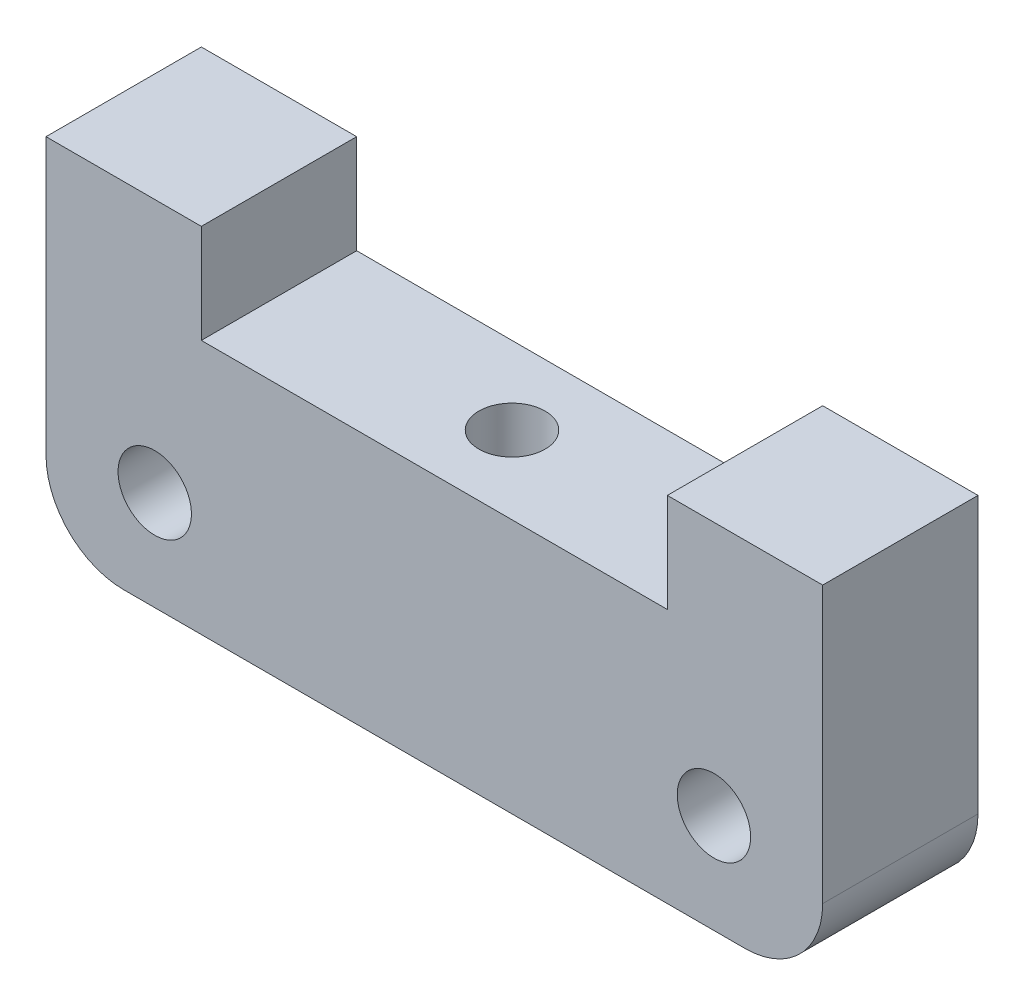
SolidWorks part; units mm, degrees
ref_plane "Front Plane" through (0, 0, 0) normal (0, 0, 1) x (1, 0, 0)
ref_plane "Top Plane" through (0, 0, 0) normal (0, 1, 0) x (1, 0, 0)
ref_plane "Right Plane" through (0, 0, 0) normal (1, 0, 0) x (0, 0, -1)
sketch "Sketch1" plane through (0, 0, 0) normal (0, 0, 1) x (1, 0, 0)
  line L0 (0, 0) -> (15.875, 0)
  line L1 (15.875, 0) -> (15.875, 14.4526)
  line L2 (15.875, 14.4526) -> (9.525, 14.4526)
  line L3 (9.525, 14.4526) -> (9.525, 10.414)
  line L4 (9.525, 10.414) -> (0, 10.414)
  line L5 (0, 10.414) -> (0, 0) construction
  line L6 (0, 10.414) -> (0, 0)
  circle A0 centre (11.43, 4.064) radius 1.5
  dimension "D1" = 3
  dimension "D2" = 4.064
  dimension "D3" = 19.05
  dimension "D4" = 6.35
  dimension "D5" = 22.86
  dimension "D6" = 4.0386
  dimension "D7" = 6.35
extrude "Boss-Extrude1" add sketch "Sketch1" along normal blind 6.35
mirror "Mirror1" about plane through (0, 10.414, 6.35) normal (1, 0, 0) of "Boss-Extrude1"
sketch "Sketch2" plane through (0, 0, 0) normal (0, -1, 0) x (1, 0, 0)
  line L0 (0, 3.175) -> (0, 0) construction
  line L1 (0, 3.175) -> (15.875, 3.175) construction
  line L2 (15.875, 6.35) -> (15.875, 0) construction
  circle A0 centre (0, 3.175) radius 1.3526
  dimension "D1" = 2.7051
extrude "Cut-Extrude1" cut sketch "Sketch2" against normal through all
fillet "Fillet1" radius 3.175 2 edges at (-15.875, 0, 3.175) (15.875, 0, 3.175)
